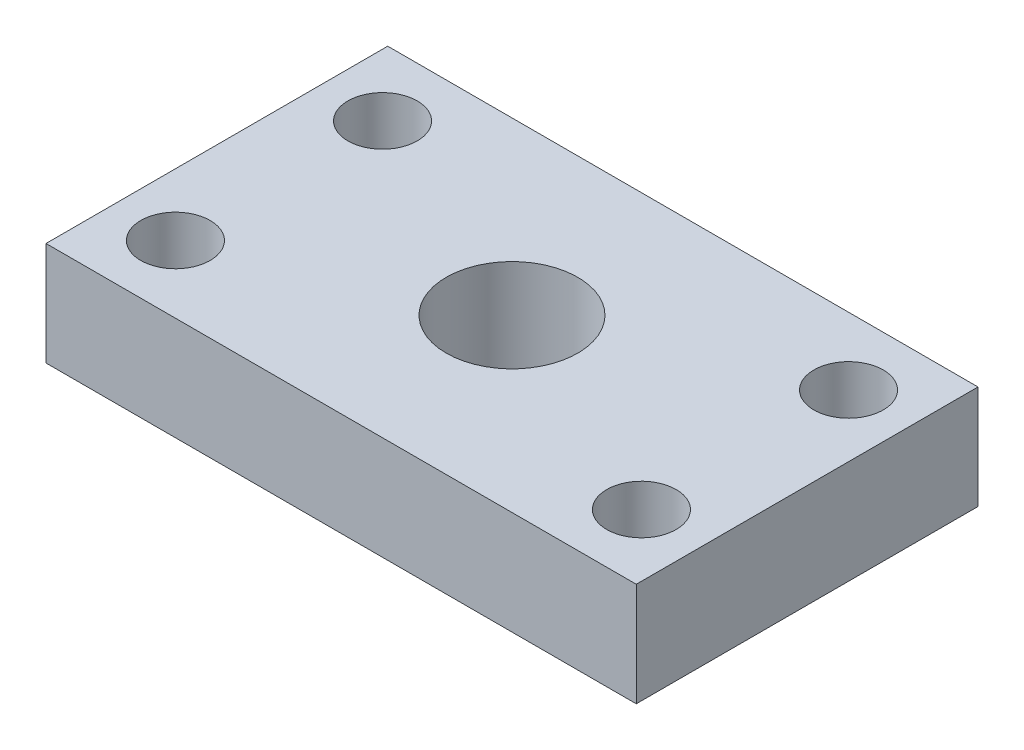
SolidWorks part; units mm, degrees
ref_plane "Front Plane" through (0, 0, 0) normal (0, 0, 1) x (1, 0, 0)
ref_plane "Top Plane" through (0, 0, 0) normal (0, 1, 0) x (1, 0, 0)
ref_plane "Right Plane" through (0, 0, 0) normal (1, 0, 0) x (0, 0, -1)
sketch "Sketch1" plane through (0, 0, 0) normal (0, 1, 0) x (1, 0, 0)
  line L1 (0, 0) -> (57, 0)
  line L2 (0, 0) -> (0, 33)
  line L3 (0, 33) -> (57, 33)
  line L4 (57, 0) -> (57, 33)
  dimension "D1" = 33
  dimension "D2" = 57
extrude "Boss-Extrude1" add sketch "Sketch1" along normal blind 10
sketch "Sketch3" plane through (0, 0, 0) normal (0, -1, 0) x (1, 0, 0)
  line L2 (0, 0) -> (57, 0) construction
  line L3 (0, -33) -> (0, 0) construction
  circle A0 centre (6, -6.5) radius 3.35
  point P4 (28.5, 0)
  point P9 (0, -16.5)
  dimension "D1" = 22.5
  dimension "D3" = 6.7
  dimension "D2" = 10
extrude "Cut-Extrude1" cut sketch "Sketch3" against normal through all
sketch "Sketch4" plane through (0, 0, 0) normal (0, -1, 0) x (1, 0, 0)
  line L2 (57, 0) -> (57, -33) construction
  line L3 (57, -33) -> (0, -33) construction
  circle A0 centre (51, -26.5) radius 3.35
  point P5 (57, -16.5)
  point P10 (28.5, -33)
  dimension "D1" = 10
  dimension "D3" = 6.7
  dimension "D2" = 22.5
extrude "Cut-Extrude2" cut sketch "Sketch4" against normal through all
ref_plane "Plane1" through (0, 0, 0) normal (1, 0, 0) x (0, 0, -1)
sketch "Sketch10" plane through (0, 0, 0) normal (0, -1, 0) x (1, 0, 0)
  line L2 (57, -33) -> (0, -33) construction
  line L3 (57, 0) -> (57, -33) construction
  circle A0 centre (6, -26.5) radius 3.35
  point P5 (28.5, -33)
  point P8 (57, -16.5)
  dimension "D1" = 22.5
  dimension "D3" = 6.7
  dimension "D2" = 10
extrude "Cut-Extrude5" cut sketch "Sketch10" against normal through all
sketch "Sketch12" plane through (0, 0, 0) normal (0, -1, 0) x (1, 0, 0)
  line L2 (57, 0) -> (57, -33) construction
  line L3 (0, 0) -> (57, 0) construction
  circle A0 centre (51, -6.5) radius 3.35
  point P5 (57, -16.5)
  point P10 (28.5, 0)
  dimension "D3" = 6.7
  dimension "D1" = 10
  dimension "D2" = 22.5
extrude "Cut-Extrude6" cut sketch "Sketch12" against normal through all
sketch "Sketch13" plane through (0, 0, -33) normal (0, 0, -1) x (-1, 0, 0)
  line L0 (-28.5, 10) -> (-28.5, 0) construction
  line L1 (-57, 10) -> (0, 10) construction
  line L2 (-57, 0) -> (0, 0) construction
  line L3 (-57, 5) -> (0, 5) construction
  line L4 (-57, 10) -> (-57, 0) construction
hole_wizard "#8-32 Tapped Hole1" positions "Sketch14" profile "Sketch15" tap size "#8-32" standard "ANSI Inch"
sketch "Sketch14" plane through (0, 0, -33) normal (0, 0, -1) x (-1, 0, 0)
  line L0 (-57, 5) -> (0, 5) construction
  line L1 (-28.5, 10) -> (-28.5, 0) construction
  point P0 (-28.5, 5)
  dimension "D1" = 0
  dimension "D2" = 0
sketch "Sketch15" plane through (28.5, 5, -33) normal (1, 0, 0) x (0, 1, 0)
  line L0 (0, 0) -> (0, 6.0378)
  line L1 (0, 6.0378) -> (1.7272, 5)
  line L2 (1.7272, 5) -> (1.7272, 0)
  line L5 (1.7272, 0) -> (0, 0)
  line L10 (0, 6.0378) -> (-1.7272, 5) construction
  line L11 (0, -6.35) -> (0, 107.95) construction
  dimension "Tap Drill Dia." = 3.4544
  dimension "Tap Drill Depth" = 5
  dimension "Drill Angle" = 118
cosmetic thread "Hole Thread1" parameters "D1"=5, "D2"=4.1656
hole_wizard "0.535-40 Tapped Hole1" positions "Sketch19" profile "Sketch18" tap size "0.535-40" standard "Thorlabs" end condition through all
sketch "Sketch19" plane through (0, 10, 0) normal (0, 1, 0) x (1, 0, 0)
  line L1 (57, 0) -> (57, 33) construction
  line L2 (28.5, 33) -> (28.5, 0) construction
  line L3 (57, 33) -> (0, 33) construction
  line L4 (0, 0) -> (57, 0) construction
  line L6 (57, 16.5) -> (0, 16.5) construction
  line L7 (0, 33) -> (0, 0) construction
  point P0 (28.5, 16.5)
  point P5 (57, 16.5)
  dimension "D1" = 0
  dimension "D2" = 0
cosmetic thread "Hole Thread3" parameters "D2"=13.589
sketch "Sketch18" plane through (28.5, 10, -16.5) normal (1, 0, 0) x (0, 0, 1)
  line L0 (0, 0) -> (0, 10)
  line L1 (0, 10) -> (6.35, 10)
  line L2 (6.35, 10) -> (6.35, 0)
  line L5 (6.35, 0) -> (0, 0)
  line L11 (0, -6.35) -> (0, 107.95) construction
  dimension "Thru Tap Drill Dia." = 12.7
  dimension "Thru Tap Drill Depth" = 10
